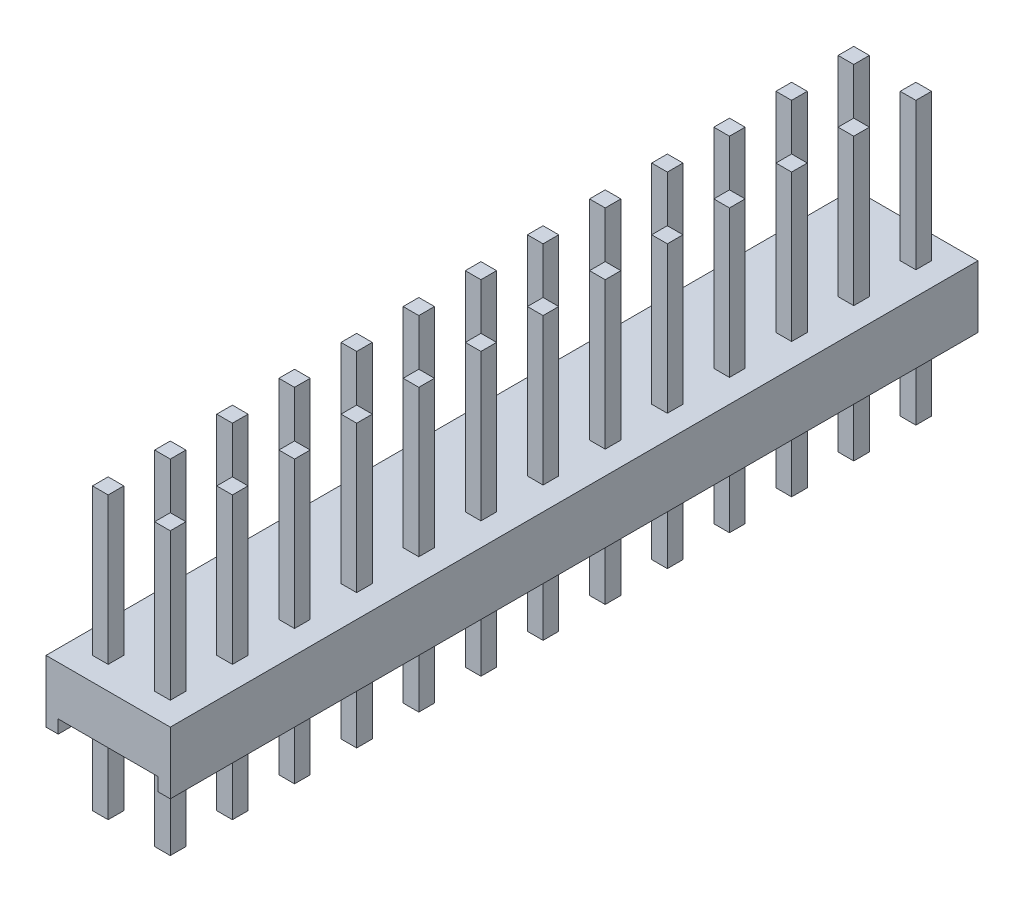
SolidWorks part; units mm, degrees
ref_plane "Спереди" through (0, 0, 0) normal (0, 0, 1) x (1, 0, 0)
ref_plane "Сверху" through (0, 0, 0) normal (0, 1, 0) x (1, 0, 0)
ref_plane "Справа" through (0, 0, 0) normal (1, 0, 0) x (0, 0, -1)
sketch "Эскиз1" plane through (0, 0, 0) normal (0, 0, 1) x (1, 0, 0)
  line L0 (-2.54, 0) -> (-2.54, 2.54)
  line L1 (-2.54, 2.54) -> (2.54, 2.54)
  line L2 (2.54, 2.54) -> (2.54, 0)
  line L3 (-2.54, 0) -> (-2.04, 0)
  line L4 (-2.04, 0) -> (-2.04, 0.54)
  line L5 (-2.04, 0.54) -> (2.04, 0.54)
  line L6 (2.04, 0.54) -> (2.04, 0)
  line L7 (2.04, 0) -> (2.54, 0)
  line L8 (-2.54, 0) -> (2.54, 0) construction
  dimension "D1" = 2.54
  dimension "D2" = 5.08
  dimension "D3" = 0.5
  dimension "D4" = 0.54
  dimension "D5" = 0.5
  dimension "D6" = 2.54
extrude "Бобышка-Вытянуть1" add sketch "Эскиз1" along normal blind 2.54
sketch "Эскиз2" plane through (0, 2.54, 0) normal (0, 1, 0) x (1, 0, 0)
  line L0 (-2.54, -1.27) -> (2.54, -1.27) construction
  line L1 (-1.59, -0.95) -> (-0.95, -0.95)
  line L2 (-1.59, -0.95) -> (-1.59, -1.59)
  line L3 (-1.59, -1.59) -> (-0.95, -1.59)
  line L4 (-0.95, -0.95) -> (-0.95, -1.59)
  line L5 (0.95, -0.95) -> (1.59, -0.95)
  line L6 (0.95, -0.95) -> (0.95, -1.59)
  line L7 (0.95, -1.59) -> (1.59, -1.59)
  line L8 (1.59, -0.95) -> (1.59, -1.59)
  line L9 (-2.54, -2.54) -> (-2.54, 0) construction
  line L12 (0, 0) -> (0, -2.54) construction
  line L13 (2.54, -2.54) -> (-2.54, -2.54) construction
  line L14 (2.54, -2.54) -> (2.54, 0) construction
  line L15 (-1.27, -1.59) -> (-1.27, -0.95) construction
  line L16 (1.27, -0.95) -> (1.27, -1.59) construction
  dimension "D1" = 0.64
  dimension "D2" = 2.54
extrude "Бобышка-Вытянуть2" add sketch "Эскиз2" along normal blind 6 and the other way blind 5.5
pattern_linear "Линейный массив27" count 13 spacing 2.54 along (0, 0, -1) of "Бобышка-Вытянуть1", "Бобышка-Вытянуть2"
